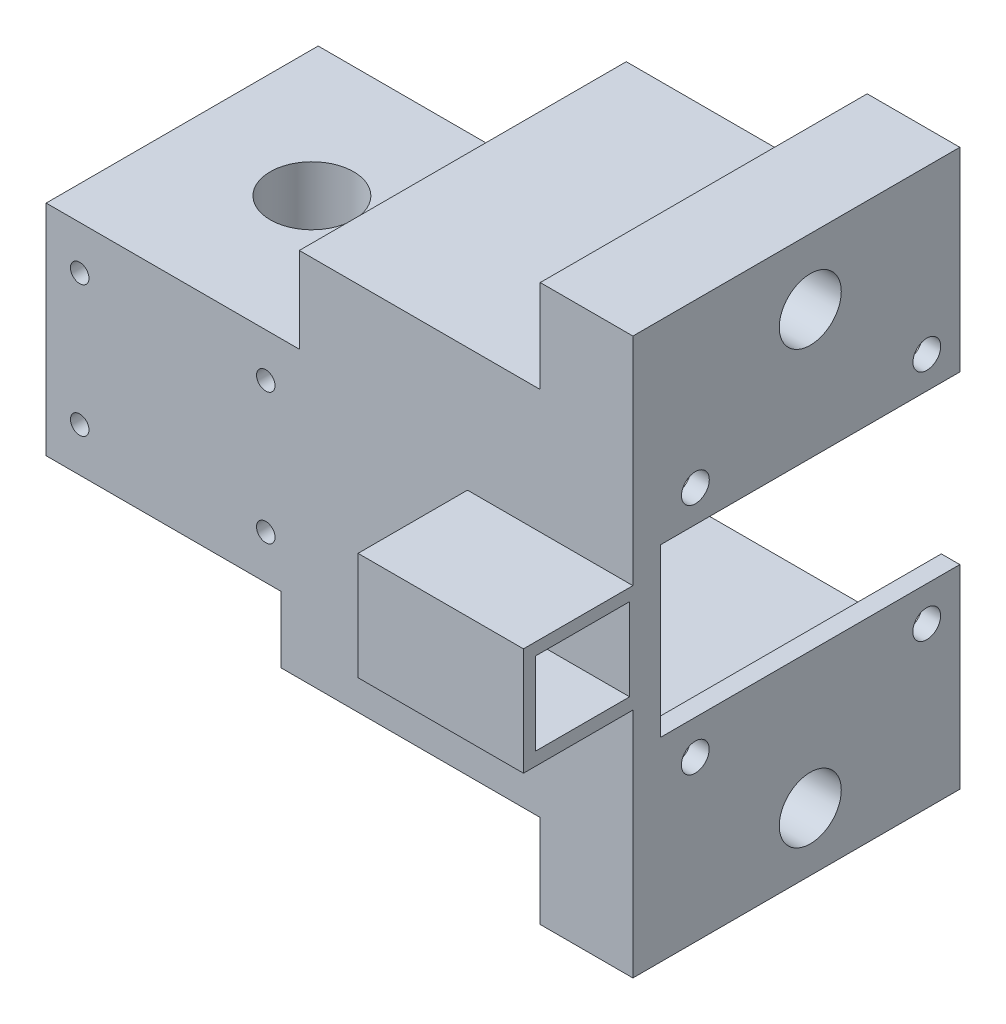
SolidWorks part; units mm, degrees
ref_plane "Front Plane" through (0, 0, 0) normal (0, 0, 1) x (1, 0, 0)
ref_plane "Top Plane" through (0, 0, 0) normal (0, 1, 0) x (1, 0, 0)
ref_plane "Right Plane" through (0, 0, 0) normal (1, 0, 0) x (0, 0, -1)
sketch "Sketch1" plane through (0, 0, -264.675) normal (0, 0, -1) x (-1, 0, 0)
  line L1 (-28.6765, -381.8964) -> (-63.3765, -381.8964)
  line L2 (-28.6765, -381.8964) -> (-28.6765, -411.8964)
  line L3 (-28.6765, -411.8964) -> (-63.3765, -411.8964)
  line L4 (-63.3765, -381.8964) -> (-63.3765, -411.8964)
extrude "Boss-Extrude1" add sketch "Sketch1" along normal up to surface (37.282 mm away)
sketch "Sketch4" plane through (0, -381.8964, 0) normal (0, 1, 0) x (1, 0, 0)
  circle A0 centre (46.0265, 283.7499) radius 5.715
  dimension "D1" = 11.43
extrude "Cut-Extrude1" cut sketch "Sketch4" against normal through all
sketch "Sketch5" plane through (0, -411.8964, 0) normal (0, -1, 0) x (1, 0, 0)
  circle A0 centre (46.4533, -275.536) radius 1.375
  circle A1 centre (54.2404, -284.1767) radius 1.375
  circle A2 centre (45.5996, -291.9638) radius 1.375
  circle A3 centre (37.8125, -283.3231) radius 1.375
  dimension "D1" = 2.75
sketch "Sketch6" plane through (0, 0, -301.957) normal (0, 0, -1) x (-1, 0, 0)
  line L0 (-29.7765, -381.8964) -> (-29.7765, -411.8964) construction
  line L1 (-63.3765, -381.8964) -> (-28.6765, -381.8964) construction
  line L2 (-28.6765, -411.8964) -> (-63.3765, -411.8964) construction
  line L3 (-62.2765, -381.8964) -> (-62.2765, -411.8964) construction
  circle A0 centre (-58.7765, -387.8964) radius 1.27
  circle A1 centre (-33.2765, -387.8964) radius 1.27
  circle A2 centre (-33.2765, -405.8964) radius 1.27
  circle A3 centre (-58.7765, -405.8964) radius 1.27
  dimension "D1" = 2.54
  dimension "D2" = 3.5
  dimension "D3" = 6
  dimension "D4" = 6
  dimension "D5" = 3.5
sketch "Sketch8" plane through (63.3765, 0, 0) normal (1, 0, 0) x (0, 0, -1)
  line L1 (268.485, -420.9724) -> (264.675, -420.9724)
  line L2 (268.485, -420.9724) -> (268.485, -370.1724)
  line L3 (268.485, -370.1724) -> (264.675, -370.1724)
  line L4 (264.675, -420.9724) -> (264.675, -370.1724)
  line L5 (268.485, -420.9724) -> (264.675, -370.1724) construction
  line L6 (268.485, -370.1724) -> (264.675, -420.9724) construction
  point P0 (266.58, -395.5724)
  dimension "D1" = 50.8
  dimension "D2" = 3.81
extrude "Boss-Extrude6" add sketch "Sketch8" along normal blind 45.72
sketch "Sketch9" plane through (0, 0, -268.485) normal (0, 0, -1) x (-1, 0, 0)
  line L0 (-63.3765, -381.8964) -> (-63.3765, -370.1724) construction
  line L1 (-109.0965, -370.1724) -> (-63.3765, -370.1724)
  line L2 (-109.0965, -370.1724) -> (-109.0965, -372.7124)
  line L3 (-106.5565, -372.7124) -> (-63.3765, -372.7124)
  line L4 (-63.3765, -370.1724) -> (-63.3765, -372.7124)
  line L6 (-109.0965, -420.9724) -> (-63.3765, -420.9724)
  line L7 (-109.0965, -420.9724) -> (-109.0965, -418.4324)
  line L8 (-106.5565, -418.4324) -> (-63.3765, -418.4324)
  line L9 (-63.3765, -420.9724) -> (-63.3765, -418.4324)
  line L10 (-106.5565, -407.0024) -> (-106.5565, -418.4324)
  line L12 (-109.0965, -372.7124) -> (-109.0965, -384.1424)
  line L14 (-106.5565, -372.7124) -> (-106.5565, -384.1424)
  line L15 (-106.5565, -384.1424) -> (-109.0965, -384.1424)
  line L17 (-106.5565, -407.0024) -> (-109.0965, -407.0024)
  line L19 (-109.0965, -407.0024) -> (-109.0965, -418.4324)
  point P14 (-106.5565, -395.5724)
  dimension "D1" = 2.54
  dimension "D2" = 2.54
  dimension "D3" = 2.54
extrude "Boss-Extrude7" add sketch "Sketch9" along normal up to surface (41 mm away)
sketch "Sketch10" plane through (109.0965, 0, 0) normal (1, 0, 0) x (0, 0, -1)
  circle A0 centre (304.9635, -379.774) radius 1.905
  circle A1 centre (304.9419, -411.7524) radius 1.905
  circle A2 centre (273.239, -379.7524) radius 1.905
  circle A3 centre (273.2219, -411.7309) radius 1.905
  dimension "D1" = 3.81
  dimension "D2" = 31.7245
  dimension "D3" = 31.72
extrude "Cut-Extrude2" cut sketch "Sketch10" against normal up to next
sketch "Sketch11" plane through (0, -370.1724, 0) normal (0, 1, 0) x (1, 0, 0)
  line L0 (109.0965, 264.675) -> (63.3765, 264.675) construction
  line L1 (109.0965, 309.485) -> (96.3965, 309.485)
  line L2 (109.0965, 309.485) -> (109.0965, 264.675)
  line L3 (109.0965, 264.675) -> (96.3965, 264.675)
  line L4 (96.3965, 309.485) -> (96.3965, 264.675)
  dimension "D1" = 12.7
extrude "Boss-Extrude8" add sketch "Sketch11" along normal blind 12.7
sketch "Sketch12" plane through (0, -420.9724, 0) normal (0, -1, 0) x (1, 0, 0)
  line L0 (109.0965, -309.485) -> (63.3765, -309.485) construction
  line L1 (109.0965, -264.675) -> (96.3965, -264.675)
  line L2 (109.0965, -264.675) -> (109.0965, -309.485)
  line L3 (109.0965, -309.485) -> (96.3965, -309.485)
  line L4 (96.3965, -264.675) -> (96.3965, -309.485)
  dimension "D1" = 12.7
extrude "Boss-Extrude9" add sketch "Sketch12" along normal blind 12.7
sketch "Sketch13" plane through (109.0965, 0, 0) normal (1, 0, 0) x (0, 0, -1)
  line L0 (264.675, -357.4724) -> (309.485, -357.4724) construction
  line L1 (288.985, -395.7524) -> (288.985, -357.4724) construction
  circle A0 centre (288.985, -366.4724) radius 4.25
  circle A1 centre (288.985, -425.6544) radius 4.25
  dimension "D3" = 8.5
  dimension "D1" = 9
  dimension "D2" = 59.182
extrude "Cut-Extrude3" cut sketch "Sketch13" against normal blind 6.35
sketch "Sketch16" plane through (0, -411.8964, 0) normal (0, -1, 0) x (1, 0, 0)
  line L0 (28.6765, -301.957) -> (63.3765, -301.957) construction
  line L1 (63.3765, -264.675) -> (60.8765, -264.675)
  line L2 (63.3765, -264.675) -> (63.3765, -301.957)
  line L3 (63.3765, -301.957) -> (60.8765, -301.957)
  line L4 (60.8765, -264.675) -> (60.8765, -301.957)
  dimension "D1" = 2.5
sketch "Sketch17" plane through (0, 0, -268.485) normal (0, 0, -1) x (-1, 0, 0)
  line L0 (-63.3765, -418.4324) -> (-106.5565, -418.4324) construction
  line L1 (-63.3765, -372.7124) -> (-66.8124, -372.7124)
  line L2 (-63.3765, -372.7124) -> (-63.3765, -418.4324)
  line L3 (-63.3765, -418.4324) -> (-66.8124, -418.4324)
  line L4 (-66.8124, -372.7124) -> (-66.8124, -418.4324)
  dimension "D1" = 3.4359
extrude "Boss-Extrude12" add sketch "Sketch17" along normal up to surface (33.472 mm away) up to face at (46.0265, -396.8964, -301.957)
extrude "Boss-Extrude11" add sketch "Sketch16" along normal up to surface (9.0761 mm away) up to face at (79.8865, -420.9724, -287.08)
sketch "Sketch21" plane through (0, 0, -309.485) normal (0, 0, -1) x (-1, 0, 0)
  line L1 (-76.8623, -444.9124) -> (-58.8878, -444.9124)
  line L2 (-76.8623, -444.9124) -> (-76.8623, -420.9724)
  line L3 (-76.8623, -420.9724) -> (-58.8878, -420.9724)
  line L4 (-58.8878, -444.9124) -> (-58.8878, -420.9724)
extrude "Boss-Extrude13" add sketch "Sketch21" against normal blind 16
sketch "Sketch22" plane through (0, 0, -309.485) normal (0, 0, -1) x (-1, 0, 0)
  line L1 (-74.2522, -423.4355) -> (-60.8727, -423.4355)
  line L2 (-74.2522, -423.4355) -> (-74.2522, -430.358)
  line L3 (-74.2522, -430.358) -> (-60.8727, -430.358)
  line L4 (-60.8727, -423.4355) -> (-60.8727, -430.358)
extrude "Cut-Extrude4" cut sketch "Sketch22" against normal through all
sketch "Sketch23" plane through (0, -444.9124, 0) normal (0, -1, 0) x (1, 0, 0)
  line L4 (73.7765, -308.585) -> (74.6765, -309.485) construction
  line L5 (61.1086, -297.5171) -> (74.4443, -297.5171)
  line L6 (61.1086, -297.5171) -> (61.1086, -309.2529)
  line L7 (61.1086, -309.2529) -> (74.4443, -309.2529)
  line L8 (74.4443, -297.5171) -> (74.4443, -309.2529)
  line L9 (61.1086, -297.5171) -> (74.4443, -309.2529) construction
  line L10 (61.1086, -309.2529) -> (74.4443, -297.5171) construction
  point P2 (67.7765, -303.385)
extrude "Cut-Extrude5" cut sketch "Sketch23" against normal up to surface (21.4769 mm away) up to face at (67.5625, -423.4355, -301.485)
sketch "Sketch24" plane through (0, 0, -264.675) normal (0, 0, 1) x (1, 0, 0)
  line L0 (109.0965, -357.4724) -> (109.0965, -433.6724) construction
  line L1 (109.0965, -387.1015) -> (86.4239, -387.1015)
  line L2 (109.0965, -387.1015) -> (109.0965, -401.8674)
  line L3 (109.0965, -401.8674) -> (86.4239, -401.8674)
  line L4 (86.4239, -387.1015) -> (86.4239, -401.8674)
extrude "Boss-Extrude14" add sketch "Sketch24" along normal blind 15
sketch "Sketch25" plane through (109.0965, 0, 0) normal (1, 0, 0) x (0, 0, -1)
  line L0 (250.875, -388.3224) -> (251.775, -389.2224) construction
  line L1 (251.325, -388.7724) -> (264.225, -388.7724)
  line L2 (251.325, -388.7724) -> (251.325, -400.0724)
  line L3 (251.325, -400.0724) -> (264.225, -400.0724)
  line L4 (264.225, -388.7724) -> (264.225, -400.0724)
  line L5 (263.775, -399.6224) -> (264.675, -400.5224) construction
extrude "Cut-Extrude6" cut sketch "Sketch25" against normal up to surface (22.6726 mm away) up to face at (86.4239, -394.4844, -257.175)
extrude "Cut-Extrude7" cut sketch "Sketch5" against normal blind 10
extrude "Cut-Extrude8" cut sketch "Sketch6" against normal through all
sketch "Sketch27" plane through (0, 0, -309.485) normal (0, 0, -1) x (-1, 0, 0)
  line L0 (-76.8623, -420.9724) -> (-76.8623, -444.9124) construction
  line L1 (-76.8623, -430.4211) -> (-58.8878, -430.4211)
  line L2 (-76.8623, -430.4211) -> (-76.8623, -444.9124)
  line L3 (-76.8623, -444.9124) -> (-58.8878, -444.9124)
  line L4 (-58.8878, -430.4211) -> (-58.8878, -444.9124)
extrude "Boss-Extrude15" add sketch "Sketch27" along normal blind 2
